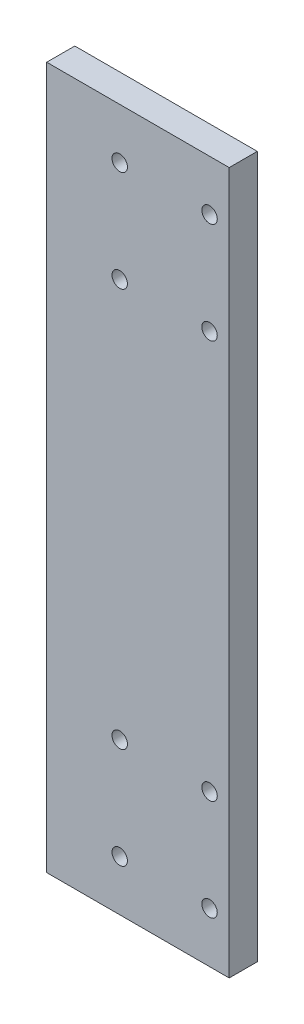
SolidWorks part; units mm, degrees
ref_plane "前视基准面" through (0, 0, 0) normal (0, 0, 1) x (1, 0, 0)
ref_plane "上视基准面" through (0, 0, 0) normal (0, 1, 0) x (1, 0, 0)
ref_plane "右视基准面" through (0, 0, 0) normal (1, 0, 0) x (0, 0, -1)
sketch "草图1" plane through (0, 0, 0) normal (0, 0, 1) x (1, 0, 0)
  line L1 (-32.5, 125) -> (32.5, 125)
  line L2 (-32.5, 125) -> (-32.5, -125)
  line L3 (-32.5, -125) -> (32.5, -125)
  line L4 (32.5, 125) -> (32.5, -125)
  line L5 (-32.5, 125) -> (32.5, -125) construction
  line L6 (-32.5, -125) -> (32.5, 125) construction
  point P0 (0, 0)
  dimension "D1" = 65
  dimension "D2" = 250
extrude "凸台-拉伸1" add sketch "草图1" along normal blind 10
sketch "草图2" plane through (0, 0, 0) normal (0, 0, -1) x (-1, 0, 0)
  line L0 (-32.5, 125) -> (32.5, 125) construction
  line L1 (-25.5, 107) -> (6.5, 107) construction
  line L2 (-25.5, 107) -> (-25.5, 71) construction
  line L3 (-25.5, 71) -> (6.5, 71) construction
  line L4 (6.5, 107) -> (6.5, 71) construction
  line L5 (-25.5, 107) -> (6.5, 71) construction
  line L6 (-25.5, 71) -> (6.5, 107) construction
  line L7 (0, 0) -> (125.8481, 0) construction
  line L8 (-25.5, -71) -> (6.5, -107) construction
  line L9 (-25.5, -107) -> (6.5, -71) construction
  line L10 (6.5, -107) -> (6.5, -71) construction
  line L11 (-25.5, -71) -> (6.5, -71) construction
  line L12 (-25.5, -107) -> (-25.5, -71) construction
  line L13 (-25.5, -107) -> (6.5, -107) construction
  point P0 (-9.5, 89)
  point P8 (0, 125)
  point P15 (-9.5, -89)
  dimension "D1" = 32
  dimension "D2" = 36
  dimension "D3" = 9.5
  dimension "D4" = 18
hole_wizard "打孔尺寸(%根据)内六角圆柱头螺钉的类型1" positions "3D草图1" profile "草图3" counterbore size "M5" standard "GB"
sketch3d "3D草图1"
  point P0 (-6.5, 107, 0)
  point P3 (25.5, 107, 0)
  point P6 (-6.5, 71, 0)
  point P9 (25.5, 71, 0)
  point P13 (25.5, -71, 0)
  point P16 (-6.5, -71, 0)
  point P19 (-6.5, -107, 0)
  point P22 (25.5, -107, 0)
sketch "草图3" plane through (-6.5, 107, 0) normal (1, 0, 0) x (0, 1, 0)
  line L0 (0, 0) -> (0, 19.6524)
  line L1 (0, 19.6524) -> (2.75, 18)
  line L2 (2.75, 18) -> (2.75, 5.7)
  line L3 (2.75, 5.7) -> (5, 5.7)
  line L4 (5, 5.7) -> (5, 0)
  line L5 (5, 0) -> (0, 0)
  line L10 (0, 19.6524) -> (-2.75, 18) construction
  line L11 (0, -6.35) -> (0, 107.95) construction
  dimension "孔直径" = 5.5
  dimension "孔深度" = 18
  dimension "柱形沉头孔直径" = 10
  dimension "柱形沉头孔深度" = 5.7
  dimension "导头角度" = 118
sketch "草图4" plane through (-32.5, 0, 0) normal (-1, 0, 0) x (0, 0, 1)
  line L0 (5, -105) -> (5, 105) construction
  line L3 (10, -125) -> (0, -125) construction
  line L5 (10, 125) -> (10, -125) construction
  line L6 (10, 125) -> (0, 125) construction
  point P9 (5, -70)
  point P22 (5, -35)
  point P23 (5, 0)
  point P24 (5, 35)
  point P25 (5, 70)
  dimension "D2" = 20
  dimension "D3" = 5
  dimension "D1" = 20
hole_wizard "M6 螺纹孔1" positions "3D草图2" profile "草图5" tap size "M6" standard "GB"
sketch3d "3D草图2"
  point P3 (-32.5, -70, 5)
  point P6 (-32.5, -35, 5)
  point P9 (-32.5, 0, 5)
  point P12 (-32.5, 35, 5)
  point P15 (-32.5, 70, 5)
  point P21 (-32.5, -105, 5)
  point P24 (-32.5, 105, 5)
sketch "草图5" plane through (-32.5, -70, 5) normal (0, 1, 0) x (0, 0, 1)
  line L0 (0, 0) -> (0, 18.5022)
  line L1 (0, 18.5022) -> (2.5, 17)
  line L2 (2.5, 17) -> (2.5, 0)
  line L5 (2.5, 0) -> (0, 0)
  line L10 (0, 18.5022) -> (-2.5, 17) construction
  line L11 (0, -6.35) -> (0, 107.95) construction
  dimension "螺纹孔钻头直径" = 5
  dimension "螺纹孔钻头深度" = 17
  dimension "导头角度" = 118
cosmetic thread "孔螺蚊线1"
cosmetic thread "孔螺蚊线2"
cosmetic thread "孔螺蚊线3"
cosmetic thread "孔螺蚊线4"
cosmetic thread "孔螺蚊线5"
cosmetic thread "孔螺蚊线6"
cosmetic thread "孔螺蚊线7"
